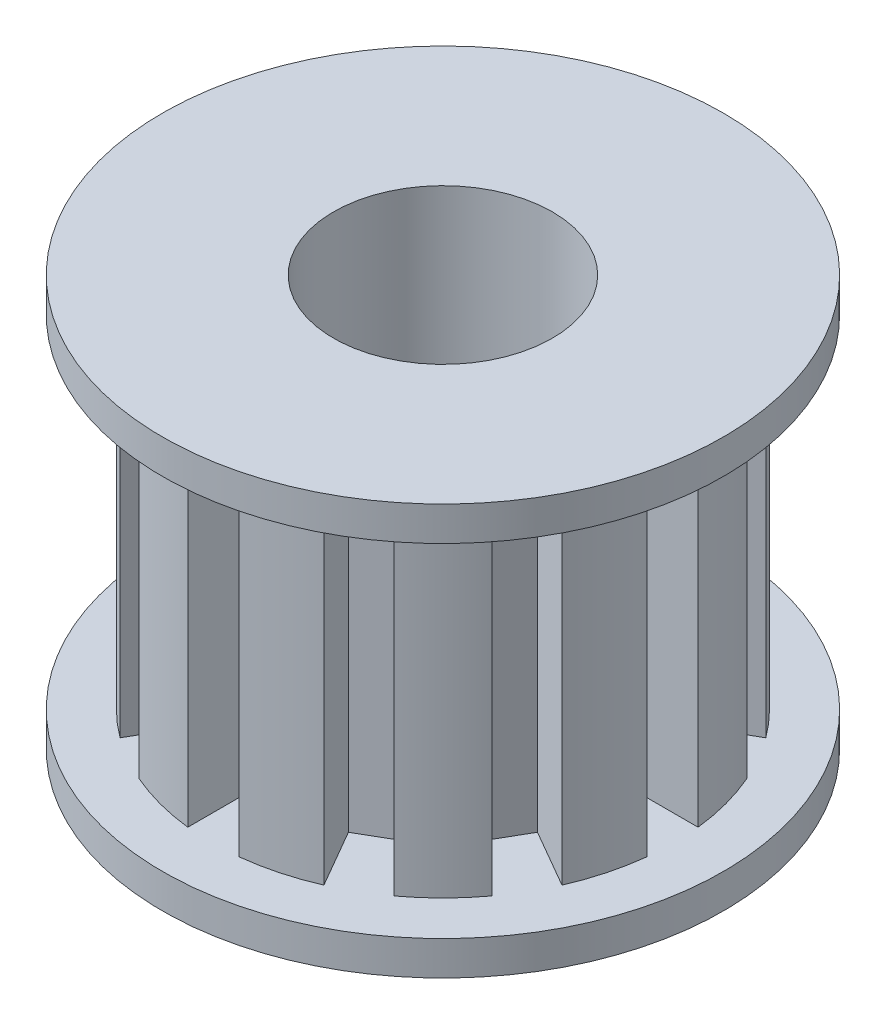
SolidWorks part; units mm, degrees
ref_plane "Front Plane" through (0, 0, 0) normal (0, 0, 1) x (1, 0, 0)
ref_plane "Top Plane" through (0, 0, 0) normal (0, 1, 0) x (1, 0, 0)
ref_plane "Right Plane" through (0, 0, 0) normal (1, 0, 0) x (0, 0, -1)
sketch "Sketch1" plane through (0, 0, 0) normal (0, 0, 1) x (1, 0, 0)
  line L0 (0, 0) -> (0, 8.9176) construction
  line L2 (3.2, 8.9176) -> (6.75, 8.9176)
  line L3 (3.2, 8.9176) -> (3.2, -3.0824)
  line L4 (3.2, -3.0824) -> (6.75, -3.0824)
  line L5 (6.75, 7.9176) -> (6.75, -2.0824)
  line L6 (6.75, 8.9176) -> (8.2, 8.9176)
  line L8 (6.75, 7.9176) -> (8.2, 7.9176)
  line L9 (8.2, 8.9176) -> (8.2, 7.9176)
  line L10 (6.75, -3.0824) -> (8.2, -3.0824)
  line L12 (6.75, -2.0824) -> (8.2, -2.0824)
  line L13 (8.2, -3.0824) -> (8.2, -2.0824)
  dimension "D1" = 3.2
  dimension "D2" = 3.55
  dimension "D3" = 0
  dimension "D4" = 0
  dimension "D5" = 5
  dimension "D6" = 5
  dimension "D7" = 1
  dimension "D8" = 1
  dimension "D9" = 10
revolve "Revolve1" add sketch "Sketch1" angle 360 about L0
ref_plane "Plane1" through (0, 0, -6.75) normal (0, 0, -1) x (-1, 0, 0)
sketch "Sketch3" plane through (0, 0, -6.75) normal (0, 0, -1) x (-1, 0, 0)
  line L0 (-8.2, 7.9176) -> (8.2, 7.9176) construction
  line L1 (-0.75, 7.9176) -> (0.75, 7.9176)
  line L2 (-0.75, 7.9176) -> (-0.75, -2.0824)
  line L3 (-0.75, -2.0824) -> (0.75, -2.0824)
  line L4 (0.75, 7.9176) -> (0.75, -2.0824)
  line L5 (0, 0) -> (0, 4.0321) construction
  dimension "D1" = 10
  dimension "D2" = 0
  dimension "D3" = 1.5
  dimension "D4" = 0.75
extrude "Cut-Extrude1" cut sketch "Sketch3" against normal blind 2
pattern_circular "CirPattern1" count 12 every 30 about axis through (0, 0, 0) along (0, 1, 0) of "Cut-Extrude1"
